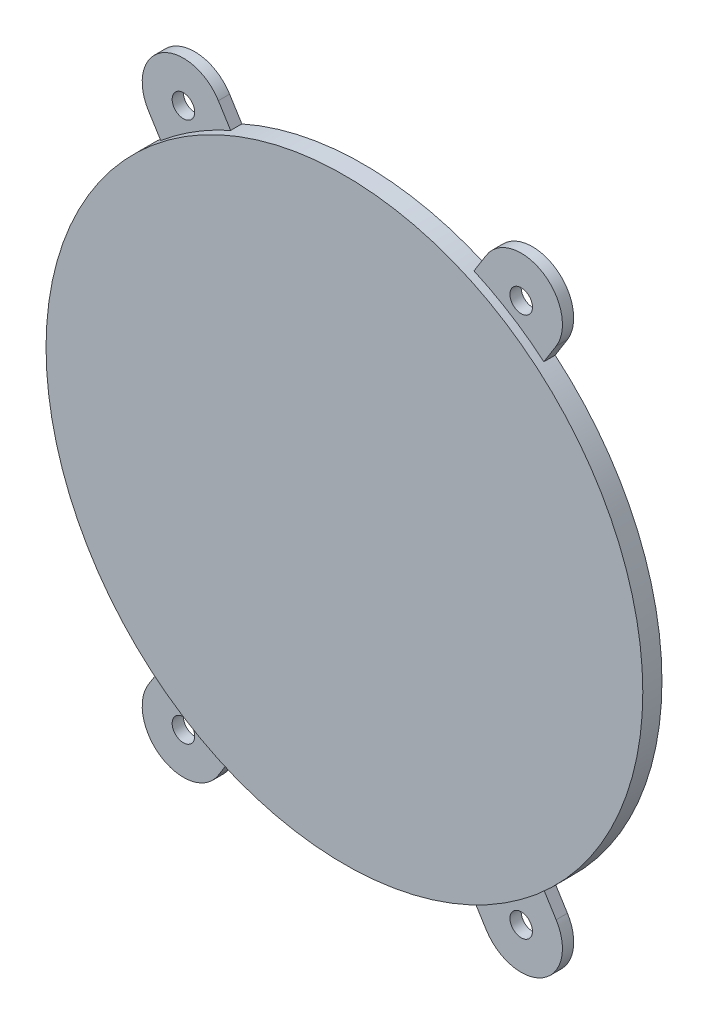
SolidWorks part; units mm, degrees
ref_plane "Спереди" through (0, 0, 0) normal (0, 0, 1) x (1, 0, 0)
ref_plane "Сверху" through (0, 0, 0) normal (0, 1, 0) x (1, 0, 0)
ref_plane "Справа" through (0, 0, 0) normal (1, 0, 0) x (0, 0, -1)
sketch "Эскиз1" plane through (0, 0, 0) normal (0, 0, 1) x (1, 0, 0)
  circle A0 centre (0, 0) radius 26.5
extrude "Бобышка-Вытянуть2" add sketch "Эскиз1" along normal blind 1.7
sketch "Эскиз3" plane through (0, 0, 0) normal (0, 0, 1) x (1, 0, 0)
  line L0 (-15, 24) -> (15, -24) construction
  line L1 (-11.8956, 25.9402) -> (18.1044, -22.0598)
  line L2 (-18.1044, 22.0598) -> (11.8956, -25.9402)
  line L3 (-15, -24) -> (15, 24) construction
  line L4 (-18.1044, -22.0598) -> (11.8956, 25.9402)
  line L5 (-11.8956, -25.9402) -> (18.1044, 22.0598)
  arc A0 (-11.8956, 25.9402) -> (-18.1044, 22.0598) centre (-15, 24) ccw
  arc A1 (11.8956, -25.9402) -> (18.1044, -22.0598) centre (15, -24) ccw
  arc A2 (-18.1044, -22.0598) -> (-11.8956, -25.9402) centre (-15, -24) ccw
  arc A3 (18.1044, 22.0598) -> (11.8956, 25.9402) centre (15, 24) ccw
  point P0 (15, 24)
  point P1 (-15, -24)
  point P2 (-15, 24)
  point P3 (15, -24)
  point P6 (0, 0)
  point P11 (0, 0)
extrude "Бобышка-Вытянуть3" add sketch "Эскиз3" along normal blind 1 contours L1 A0 L2 L4 | L5 A3 L4 L1 | L4 A2 L5 L2 | L2 A1 L1 L5
sketch "Эскиз4" plane through (0, 0, 1) normal (0, 0, 1) x (1, 0, 0)
  circle A0 centre (-15, 24) radius 1
  circle A1 centre (15, 24) radius 1
  circle A2 centre (15, -24) radius 1
  circle A3 centre (-15, -24) radius 1
extrude "Вырез-Вытянуть1" cut sketch "Эскиз4" against normal blind 1
